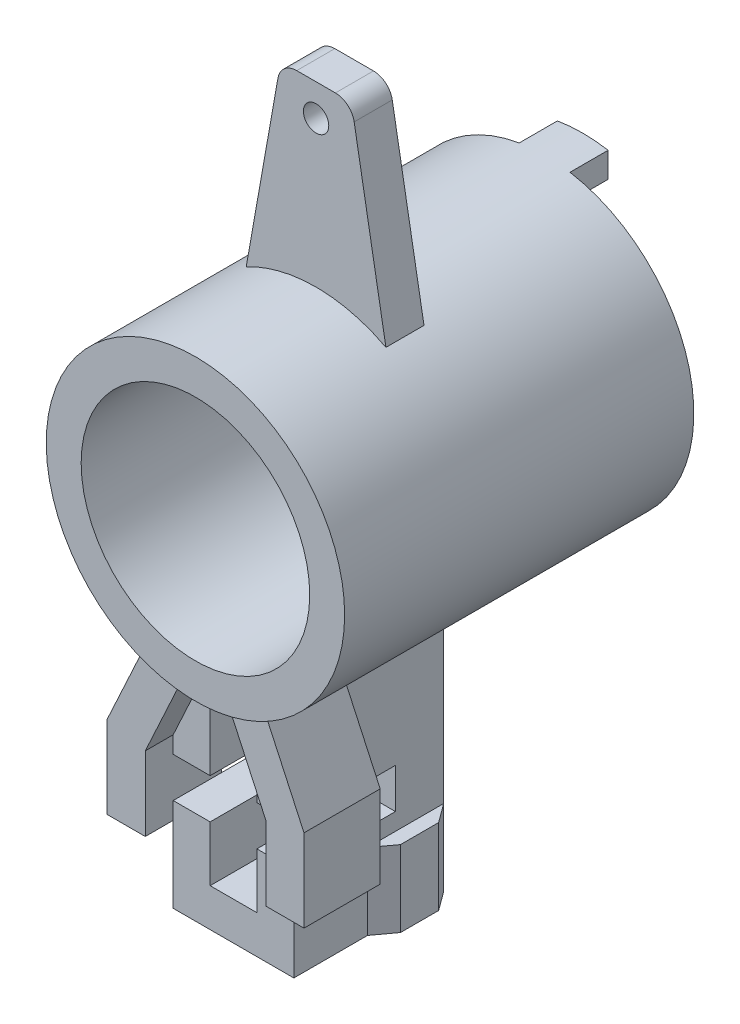
SolidWorks part; units mm, degrees
ref_plane "Plane1" through (0, 0, 0) normal (0, 0, 1) x (1, 0, 0)
ref_plane "Plane2" through (0, 0, 0) normal (0, 1, 0) x (1, 0, 0)
ref_plane "Plane3" through (0, 0, 0) normal (1, 0, 0) x (0, 0, -1)
sketch "Sketch1" plane through (0, 0, 0) normal (0, 0, 1) x (1, 0, 0)
  circle A0 centre (0, 0) radius 5.969
  circle A1 centre (0, 0) radius 4.572
  dimension "D1" = 9.144
  dimension "D2" = 11.938
extrude "Base-Extrude" add sketch "Sketch1" along normal blind 13.97
ref_plane "Plane4" through (0, 0, 13.5636) normal (0, 0, 1) x (1, 0, 0)
extrude "Boss-Extrude1" add sketch "Sketch2" against normal blind 7.112
sketch "Sketch2" plane through (0, 0, 13.5636) normal (0, 0, 1) x (1, 0, 0)
  line L0 (-2.413, -5.4595) -> (-3.937, -8.763)
  line L1 (-3.937, -8.763) -> (-3.937, -12.065)
  line L2 (-3.937, -12.065) -> (-2.413, -12.065)
  line L3 (3.937, -12.065) -> (3.937, -8.763)
  line L4 (3.937, -8.763) -> (2.413, -5.4595)
  line L5 (-2.413, -12.065) -> (-2.413, -15.113)
  line L6 (-2.413, -15.113) -> (2.413, -15.113)
  line L7 (2.413, -15.113) -> (2.413, -12.065)
  line L8 (2.413, -12.065) -> (3.937, -12.065)
  line L9 (0, -15.113) -> (0, 0) construction
  circle A0 centre (0, 0) radius 5.969 construction
  circle A2 centre (0, 0) radius 5.969
  arc A3 (-2.413, -5.4595) -> (2.413, -5.4595) centre (0, 0) ccw
  dimension "D1" = 21.082
  dimension "D2" = 3.048
  dimension "D3" = 3.302
  dimension "D4" = 4.826
  dimension "D5" = 7.874
  dimension "D6" = 4.826
  dimension "D7" = 0
sketch "Sketch3" plane through (0, 0, 13.97) normal (0, 0, 1) x (1, 0, 0)
  line L0 (2.413, -12.065) -> (-2.413, -12.065)
  line L1 (2.413, -15.113) -> (2.413, -12.065) construction
  line L2 (-2.413, -15.113) -> (2.413, -15.113) construction
  line L3 (-2.413, -12.065) -> (-2.413, -15.113) construction
  line L4 (2.413, -15.113) -> (2.413, -12.065)
  line L5 (-2.413, -15.113) -> (2.413, -15.113)
  line L6 (-2.413, -12.065) -> (-2.413, -15.113)
extrude "Cut-Extrude1" cut sketch "Sketch3" against normal blind 1.524
sketch "Sketch4" plane through (0, -12.065, 0) normal (0, -1, 0) x (1, 0, 0)
  line L0 (2.413, 10.5156) -> (3.937, 10.5156)
  line L1 (2.413, 6.4516) -> (2.413, 12.446) construction
  line L2 (3.937, 6.4516) -> (3.937, 13.5636) construction
  line L3 (-2.413, 10.5156) -> (-3.937, 10.5156)
  line L4 (-2.413, 6.4516) -> (-2.413, 12.446) construction
  line L5 (-3.937, 6.4516) -> (-3.937, 13.5636) construction
  line L6 (2.413, 6.4516) -> (3.937, 6.4516) construction
  line L7 (-3.937, 6.4516) -> (-2.413, 6.4516) construction
  line L8 (3.937, 6.4516) -> (3.937, 10.5156)
  line L9 (2.413, 6.4516) -> (3.937, 6.4516)
  line L10 (2.413, 6.4516) -> (2.413, 10.5156)
  line L11 (-3.937, 6.4516) -> (-3.937, 10.5156)
  line L12 (-3.937, 6.4516) -> (-2.413, 6.4516)
  line L13 (-2.413, 6.4516) -> (-2.413, 10.5156)
  dimension "D1" = 4.064
extrude "Cut-Extrude2" cut sketch "Sketch4" against normal up to vertex
sketch "Sketch5" plane through (2.413, 0, 0) normal (1, 0, 0) x (0, 0, -1)
  line L0 (-6.4516, -15.113) -> (-12.446, -15.113) construction
  line L1 (-10.5156, -5.4595) -> (-10.5156, -12.065) construction
  circle A0 centre (-9.7155, -10.5775) radius 0.8001
  dimension "D1" = 1.6002
  dimension "D2" = 4.5355
extrude "Cut-Extrude3" cut sketch "Sketch5" against normal up to next
ref_plane "Plane5" through (0, 0, 9.144) normal (0, 0, 1) x (1, 0, 0)
sketch "Sketch6" plane through (0, 0, 9.144) normal (0, 0, 1) x (1, 0, 0)
  line L0 (-2.794, 5.2747) -> (-1.524, 12.4518)
  line L1 (2.794, 5.2747) -> (1.524, 12.4518)
  line L2 (0.7737, 13.081) -> (-0.7737, 13.081)
  line L3 (0, 0) -> (0, 13.081) construction
  circle A0 centre (0, 0) radius 5.969 construction
  arc A1 (0.7737, 13.081) -> (1.524, 12.4518) centre (0.7737, 12.319) cw
  arc A2 (-0.7737, 13.081) -> (-1.524, 12.4518) centre (-0.7737, 12.319) ccw
  circle A4 centre (0, 0) radius 5.969
  arc A5 (2.794, 5.2747) -> (-2.794, 5.2747) centre (0, 0) ccw
  dimension "D1" = 0.762
  dimension "D2" = 5.588
  dimension "D3" = 19.05
  dimension "D4" = 3.048
  dimension "D5" = 0
extrude "Boss-Extrude2" add sketch "Sketch6" against normal blind 1.524
sketch "Sketch7" plane through (0, 0, 9.144) normal (0, 0, 1) x (1, 0, 0)
  line L0 (0.7737, 13.081) -> (-0.7737, 13.081) construction
  circle A0 centre (0, 11.811) radius 0.508
  dimension "D2" = 1.016
  dimension "D1" = 1.27
extrude "Cut-Extrude4" cut sketch "Sketch7" against normal through all
sketch "Sketch8" plane through (0, 0, 0) normal (0, 0, -1) x (-1, 0, 0)
  line L0 (-1.016, 4.8736) -> (-1.016, 5.8819)
  line L1 (1.016, 4.8736) -> (1.016, 5.8819)
  circle A0 centre (0, 0) radius 5.969 construction
  circle A1 centre (0, 0) radius 4.9784
  arc A2 (1.016, 4.8736) -> (-1.016, 4.8736) centre (0, 0) ccw
  arc A3 (1.016, 5.8819) -> (-1.016, 5.8819) centre (0, 0) ccw
  dimension "D2" = 2.032
  dimension "D3" = 1.016
  dimension "D1" = 0.4064
extrude "Boss-Extrude3" add sketch "Sketch8" along normal blind 1.524
sketch "Sketch9" plane through (0, -15.113, 0) normal (0, -1, 0) x (1, 0, 0)
  line L0 (0, 6.4516) -> (0, 12.446) construction
  line L1 (0, 13.5636) -> (0, 6.4516) construction
  line L2 (-2.413, 12.446) -> (2.413, 12.446) construction
  line L3 (-2.413, 6.4516) -> (2.413, 6.4516) construction
  line L4 (2.413, 9.4996) -> (2.9718, 8.7376)
  line L5 (-2.413, 9.4996) -> (-2.9718, 8.7376)
  line L6 (2.9718, 8.7376) -> (2.9718, 7.2136)
  line L7 (-2.9718, 8.7376) -> (-2.9718, 7.2136)
  line L8 (2.9718, 7.2136) -> (2.413, 6.4516)
  line L9 (2.413, 6.4516) -> (2.413, 12.446) construction
  line L10 (-2.9718, 7.2136) -> (-2.413, 6.4516)
  line L11 (-2.413, 6.4516) -> (2.413, 6.4516) construction
  line L12 (2.413, 6.4516) -> (2.413, 9.4996)
  line L13 (-2.413, 6.4516) -> (-2.413, 12.446) construction
  line L14 (-2.413, 6.4516) -> (-2.413, 9.4996)
  dimension "D1" = 5.9436
  dimension "D2" = 3.048
  dimension "D3" = 1.524
extrude "Boss-Extrude4" add sketch "Sketch9" along normal up to surface (3.048 mm away)
sketch "Sketch10" plane through (0, 0, 13.5636) normal (0, 0, 1) x (1, 0, 0)
  line L0 (-3.937, -12.065) -> (3.937, -12.065) construction
  line L1 (-2.413, -12.065) -> (2.413, -12.065)
  line L5 (-2.413, -10.541) -> (2.413, -10.541)
  line L6 (2.413, -10.541) -> (2.413, -9.0976)
  line L7 (2.413, -9.0976) -> (1.5937, -7.3216)
  line L8 (-1.5937, -7.3216) -> (-2.413, -9.0976)
  line L9 (-2.413, -9.0976) -> (-2.413, -10.541)
  line L11 (2.413, -12.065) -> (2.413, -9.0976)
  line L12 (2.413, -9.0976) -> (0.9356, -5.8952)
  line L13 (-0.9356, -5.8952) -> (-2.413, -9.0976)
  line L14 (-2.413, -9.0976) -> (-2.413, -12.065)
  circle A0 centre (0, 0) radius 5.969 construction
  arc A1 (-1.5937, -7.3216) -> (1.5937, -7.3216) centre (0, 0) ccw
  arc A2 (-0.9356, -5.8952) -> (0.9356, -5.8952) centre (0, 0) ccw
  dimension "D1" = 1.524
extrude "Cut-Extrude5" cut sketch "Sketch10" against normal up to surface (1.1176 mm away)
sketch "Sketch12" plane through (0, 0, 12.446) normal (0, 0, 1) x (1, 0, 0)
  line L2 (0.9356, -5.8952) -> (0.9356, -9.7774)
  line L3 (-0.9356, -5.8952) -> (-0.9356, -9.7774)
  line L5 (2.413, -12.065) -> (2.413, -9.0976) construction
  line L6 (-2.413, -9.0976) -> (-2.413, -12.065) construction
  line L7 (-2.413, -11.3776) -> (2.413, -11.3776) construction
  line L8 (2.413, -9.7774) -> (-2.413, -9.7774) construction
  line L11 (2.413, -11.3776) -> (2.413, -9.7774)
  line L12 (-2.413, -9.7774) -> (-2.413, -11.3776)
  line L13 (-2.413, -11.3776) -> (-0.9356, -11.3776)
  line L14 (2.413, -9.7774) -> (0.9356, -9.7774)
  line L15 (-0.9356, -13.589) -> (0.9356, -13.589)
  line L16 (-0.9356, -9.7774) -> (-2.413, -9.7774)
  line L17 (0.9356, -11.3776) -> (2.413, -11.3776)
  line L18 (-0.9356, -11.3776) -> (-0.9356, -13.589)
  line L19 (0.9356, -11.3776) -> (0.9356, -13.589)
  circle A1 centre (0, 0) radius 5.969 construction
  arc A2 (-0.9356, -5.8952) -> (0.9356, -5.8952) centre (0, 0) ccw
  dimension "D1" = 1.524
extrude "Cut-Extrude6" cut sketch "Sketch12" against normal blind 4.064
